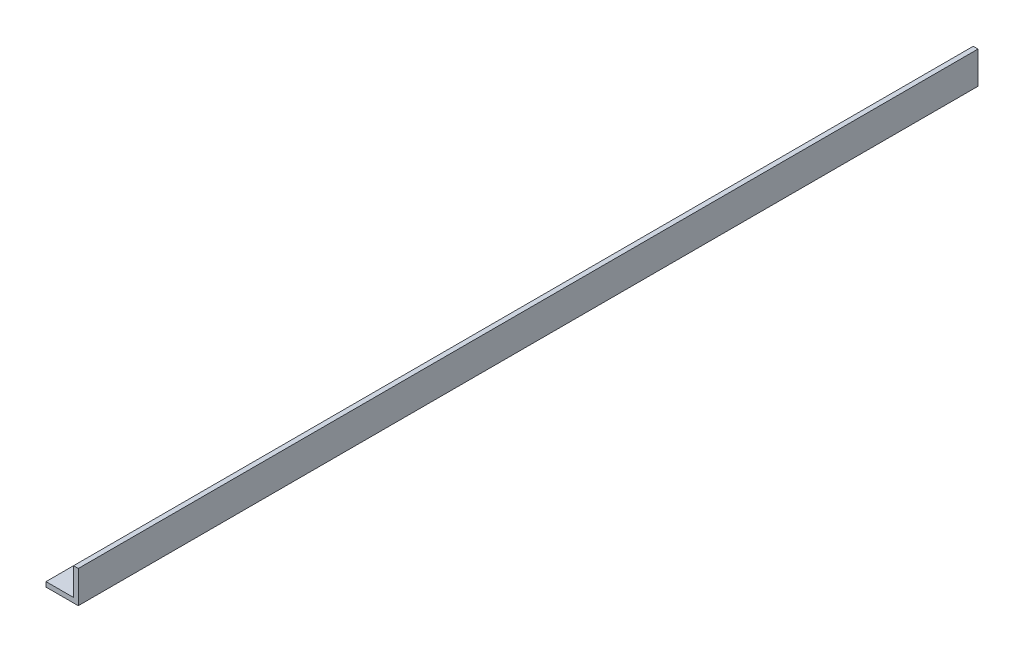
SolidWorks part; units mm, degrees
material "6061 Alloy"
ref_plane "Front" through (0, 0, 0) normal (0, 0, 1) x (1, 0, 0)
ref_plane "Top" through (0, 0, 0) normal (0, 1, 0) x (1, 0, 0)
ref_plane "Right" through (0, 0, 0) normal (1, 0, 0) x (0, 0, -1)
sketch "Sketch1" plane through (0, 0, 0) normal (0, 0, 1) x (1, 0, 0)
  line L0 (0, 0) -> (27, 0)
  line L1 (27, 0) -> (27, 27)
  line L2 (0, 4) -> (23, 4)
  line L3 (23, 4) -> (23, 27)
  line L4 (23, 27) -> (27, 27)
  line L5 (0, 4) -> (0, 0)
  dimension "D1" = 27
  dimension "D2" = 4
extrude "Boss-Extrude1" add sketch "Sketch1" along normal blind 753
